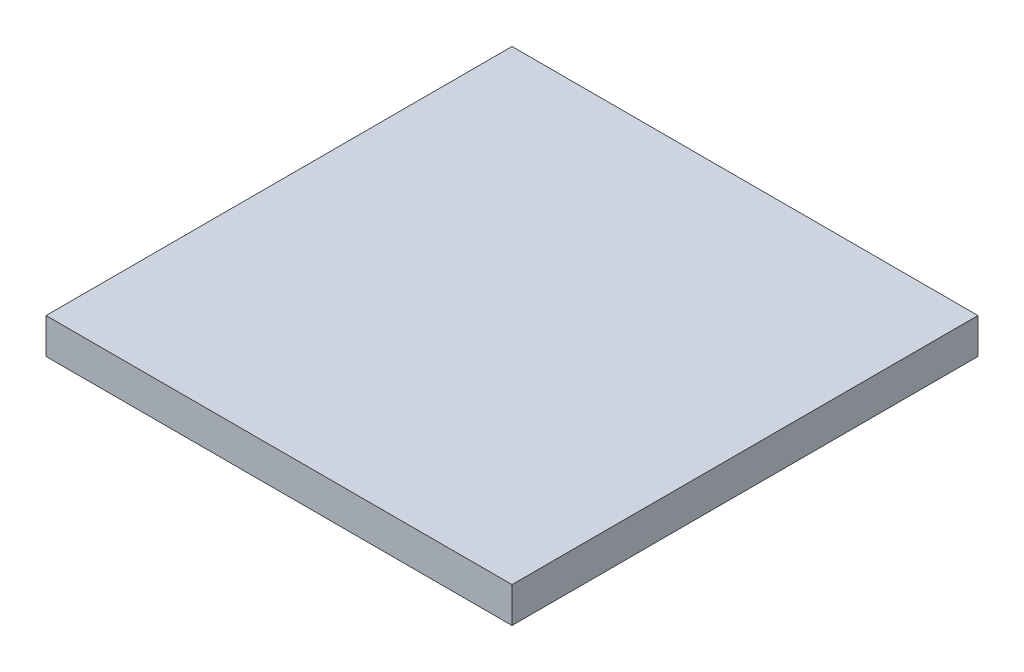
SolidWorks part; units mm, degrees
ref_plane "Front Plane" through (0, 0, 0) normal (0, 0, 1) x (1, 0, 0)
ref_plane "Top Plane" through (0, 0, 0) normal (0, 1, 0) x (1, 0, 0)
ref_plane "Right Plane" through (0, 0, 0) normal (1, 0, 0) x (0, 0, -1)
sketch "Sketch2" plane through (0, 0, 0) normal (0, 1, 0) x (1, 0, 0)
  line L1 (0, 7.7627) -> (-131.4483, 7.7627)
  line L2 (0, 7.7627) -> (0, 139.2127)
  line L3 (0, 139.2127) -> (-131.4483, 139.2127)
  line L4 (-131.4483, 7.7627) -> (-131.4483, 139.2127)
  dimension "D1" = 131.4483
  dimension "D2" = 131.45
extrude "Boss-Extrude2" add sketch "Sketch2" along normal blind 10
